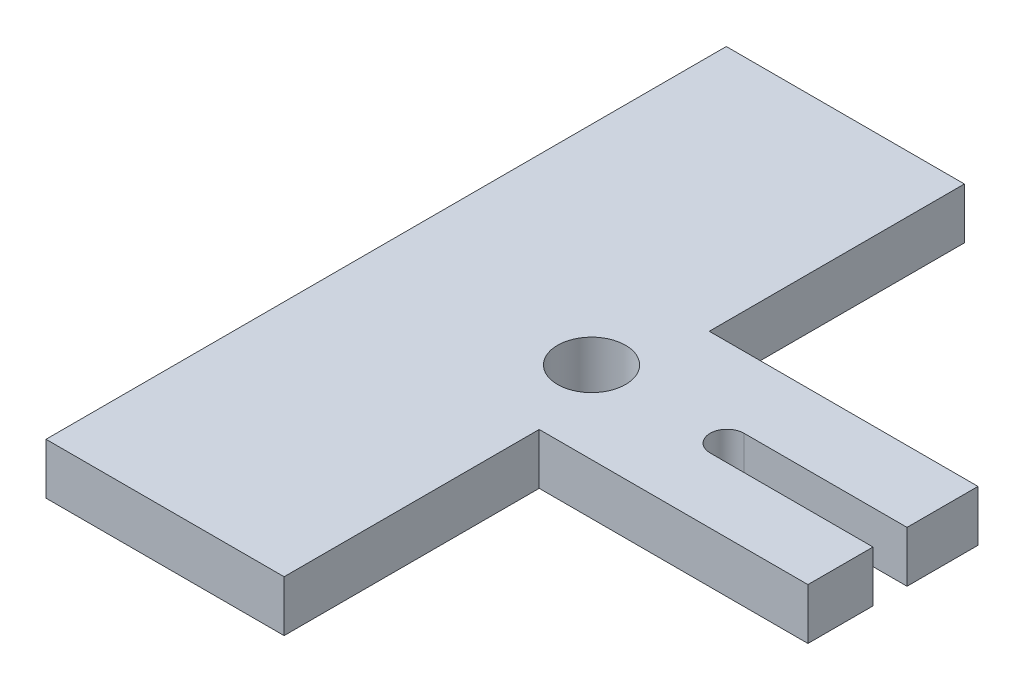
SolidWorks part; units mm, degrees
ref_plane "Front Plane" through (0, 0, 0) normal (0, 0, 1) x (1, 0, 0)
ref_plane "Top Plane" through (0, 0, 0) normal (0, 1, 0) x (1, 0, 0)
ref_plane "Right Plane" through (0, 0, 0) normal (1, 0, 0) x (0, 0, -1)
sketch "Sketch1" plane through (0, 0, 0) normal (0, 1, 0) x (1, 0, 0)
  line L1 (-16.2464, 13.7249) -> (-1.2464, 13.7249)
  line L2 (-16.2464, 13.7249) -> (-16.2464, -6.2751)
  line L3 (-16.2464, -6.2751) -> (-1.2464, -6.2751)
  line L4 (-1.2464, 13.7249) -> (-1.2464, -6.2751)
  line L5 (-16.2464, 13.7249) -> (-1.2464, -6.2751) construction
  line L6 (-16.2464, -6.2751) -> (-1.2464, 13.7249) construction
  point P0 (-8.7464, 3.7249)
  dimension "D1" = 20
  dimension "D2" = 15
extrude "Boss-Extrude1" add sketch "Sketch1" along normal blind 1.5
sketch "Sketch2" plane through (0, 1.5, 0) normal (0, 1, 0) x (1, 0, 0)
  line L0 (-16.121, 3.6384) -> (-10.121, 3.6384)
  circle A0 centre (-10.121, 3.6384) radius 1
  point P2 (0, 0)
  dimension "D1" = 2
  dimension "D2" = 0
extrude "Cut-Extrude1" cut sketch "Sketch2" against normal blind 1.5 contours A0
sketch "Sketch3" plane through (0, 1.5, 0) normal (0, 1, 0) x (1, 0, 0)
  line L0 (-9.2464, -6.2751) -> (-9.2464, -7.4825)
  line L1 (-1.2464, -6.2751) -> (-1.2464, 13.7249) construction
  line L2 (-16.2464, -6.2751) -> (-1.2464, -6.2751) construction
  line L3 (-9.2464, -6.2751) -> (-9.2464, 1.2249)
  line L4 (-9.2464, 13.7249) -> (-9.2464, 6.2249)
  line L8 (-9.2464, 1.2249) -> (-1.3464, 1.2249)
  line L9 (-9.2464, 6.2249) -> (-1.3464, 6.2249)
  line L13 (-1.3464, 6.2249) -> (-1.3464, 1.2249)
  line L14 (-9.2464, -7.4825) -> (1.993, -6.056)
  line L15 (1.993, -6.056) -> (1.993, 15.1513)
  line L16 (1.993, 15.1513) -> (-9.2464, 13.7249)
  point P1 (4.993, 15.1513)
  point P10 (0, 0)
  dimension "D1" = 7.5
  dimension "D2" = 7.5
  dimension "D3" = 8
  dimension "D4" = 0.1
extrude "Cut-Extrude2" cut sketch "Sketch3" against normal blind 1.5 contours L16 L4 L9 L13 L8 L3 L0 L14 L15
sketch "Sketch4" plane through (0, 1.5, 0) normal (0, 1, 0) x (1, 0, 0)
  line L0 (-19.0628, 3.6384) -> (1.545, 3.6384) construction
  line L1 (-9.2464, 1.2249) -> (-1.3464, 1.2249) construction
  line L2 (-6.1368, 4.1384) -> (-0.9663, 4.1384)
  line L3 (-0.9663, 4.1384) -> (-0.9663, 3.1384)
  line L4 (-0.9663, 3.1384) -> (-6.1368, 3.1384)
  line L5 (-1.3464, 6.2249) -> (-1.3464, 1.2249) construction
  arc A0 (-6.1368, 4.1384) -> (-6.1368, 3.1384) centre (-6.1368, 3.6384) ccw
  dimension "D2" = 1
  dimension "D1" = 4.7904
extrude "Cut-Extrude3" cut sketch "Sketch4" against normal blind 1.5 contours L2 L3 L4 A0
